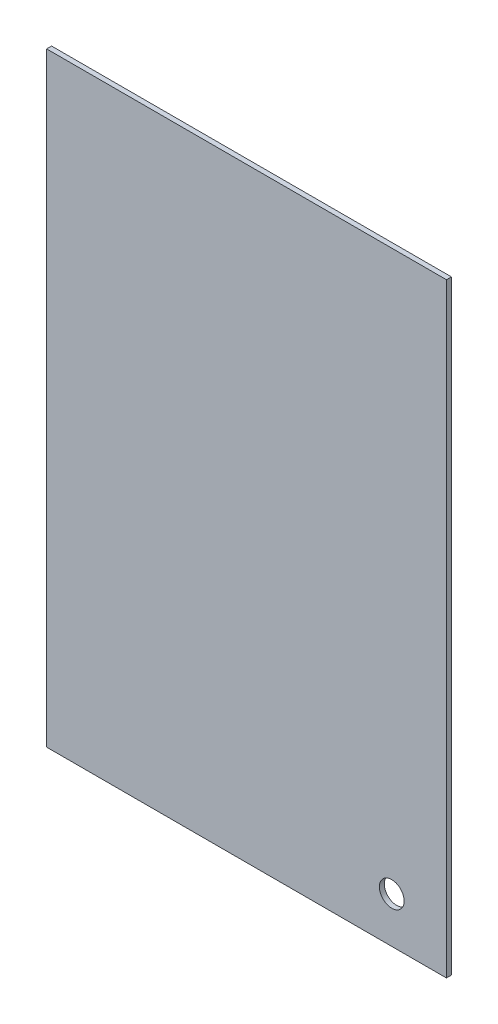
SolidWorks part; units mm, degrees
ref_plane "Alzado" through (0, 0, 0) normal (0, 0, 1) x (1, 0, 0)
ref_plane "Planta" through (0, 0, 0) normal (0, 1, 0) x (1, 0, 0)
ref_plane "Vista lateral" through (0, 0, 0) normal (1, 0, 0) x (0, 0, -1)
sketch "Sketch1" plane through (0, 0, 0) normal (0, 0, 1) x (1, 0, 0)
  line L1 (-121, 183) -> (121, 183)
  line L2 (-121, 183) -> (-121, -183)
  line L3 (-121, -183) -> (121, -183)
  line L4 (121, 183) -> (121, -183)
  line L5 (-121, 183) -> (121, -183) construction
  line L6 (-121, -183) -> (121, 183) construction
  point P0 (0, 0)
  dimension "D1" = 242
  dimension "D2" = 366
extrude "Boss-Extrude1" add sketch "Sketch1" along normal blind 3
sketch "Sketch2" plane through (0, 0, 3) normal (0, 0, 1) x (1, 0, 0)
  circle A0 centre (87.9, -155.5) radius 7.5
  dimension "D1" = 15
extrude "Cut-Extrude1" cut sketch "Sketch2" against normal up to next
